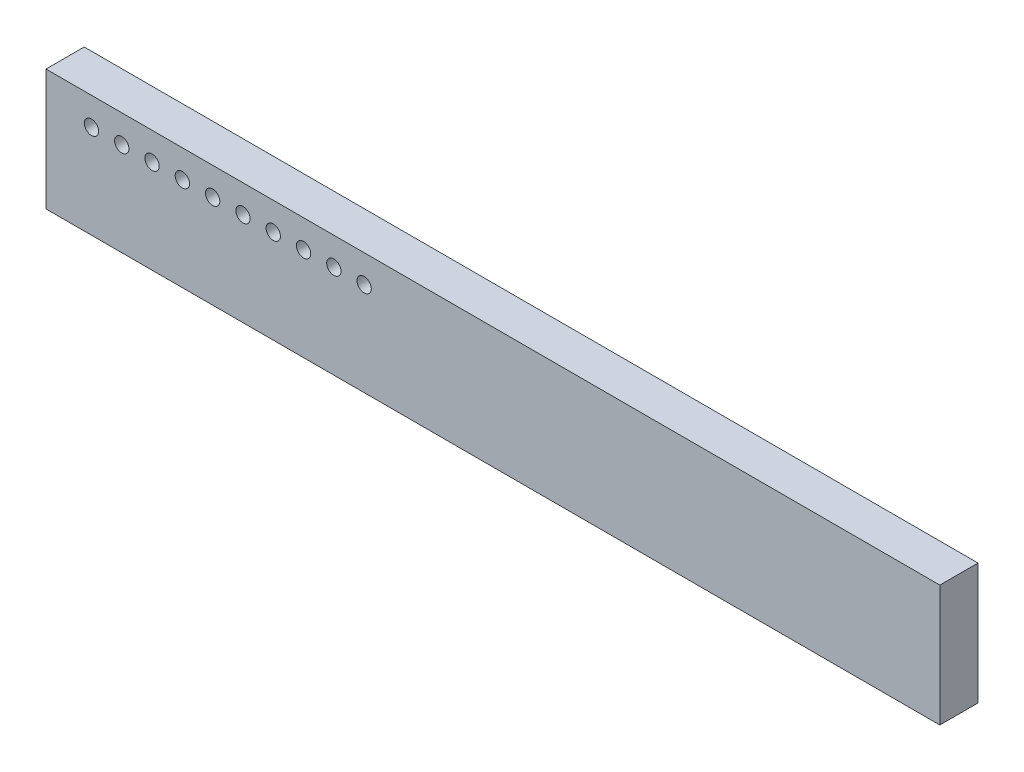
SolidWorks part; units mm, degrees
ref_plane "Front Plane" through (0, 0, 0) normal (0, 0, 1) x (1, 0, 0)
ref_plane "Top Plane" through (0, 0, 0) normal (0, 1, 0) x (1, 0, 0)
ref_plane "Right Plane" through (0, 0, 0) normal (1, 0, 0) x (0, 0, -1)
sketch "Sketch1" plane through (0, 0, 0) normal (0, 0, 1) x (1, 0, 0)
  line L1 (-18.7325, -2.54) -> (18.7325, -2.54)
  line L2 (-18.7325, -2.54) -> (-18.7325, 2.54)
  line L3 (-18.7325, 2.54) -> (18.7325, 2.54)
  line L4 (18.7325, -2.54) -> (18.7325, 2.54)
  line L5 (-18.7325, -2.54) -> (18.7325, 2.54) construction
  line L6 (-18.7325, 2.54) -> (18.7325, -2.54) construction
  point P0 (0, 0)
  dimension "D1" = 37.465
  dimension "D2" = 5.08
extrude "Boss-Extrude1" add sketch "Sketch1" along normal blind 1.6
sketch "Sketch2" plane through (0, 0, 1.6) normal (0, 0, 1) x (1, 0, 0)
  line L0 (-5.4725, 1.455) -> (-5.3225, 1.305) construction
  line L1 (-18.7325, 2.54) -> (-18.7325, -2.54) construction
  line L2 (18.7325, 2.54) -> (-18.7325, 2.54) construction
  line L4 (-5.3225, 1.455) -> (-5.4725, 1.455)
  line L5 (-5.4725, 1.455) -> (-5.4725, 1.305)
  line L6 (-5.4725, 1.305) -> (-5.3225, 1.305)
  line L7 (-5.3225, 1.305) -> (-5.3225, 1.455)
  line L8 (-5.3225, 1.455) -> (-5.4725, 1.455)
  line L9 (-5.4725, 1.455) -> (-5.4725, 1.305)
  line L10 (-5.4725, 1.305) -> (-5.3225, 1.305)
  line L11 (-5.3225, 1.305) -> (-5.3225, 1.455)
  circle A0 centre (-5.3975, 1.38) radius 0.3
  circle A1 centre (-6.6675, 1.38) radius 0.3
  circle A2 centre (-7.9375, 1.38) radius 0.3
  circle A3 centre (-9.2075, 1.38) radius 0.3
  circle A4 centre (-10.4775, 1.38) radius 0.3
  circle A5 centre (-11.7475, 1.38) radius 0.3
  circle A6 centre (-13.0175, 1.38) radius 0.3
  circle A7 centre (-14.2875, 1.38) radius 0.3
  circle A8 centre (-15.5575, 1.38) radius 0.3
  circle A9 centre (-16.8275, 1.38) radius 0.3
  dimension "D2" = 10
  dimension "D5" = 0.6
  dimension "D3" = 1.905
  dimension "D4" = 1.16
  dimension "D1" = 0
extrude "Cut-Extrude1" cut sketch "Sketch2" against normal blind 2.54
sketch "Sketch3" plane through (0, 0, 1.6) normal (0, 0, 1) x (1, 0, 0)
  line L0 (-18.7325, 2.54) -> (-16.1925, 0) construction
  line L1 (-16.1925, 0) -> (-18.7325, -2.54) construction
  line L2 (0, 2.54) -> (0, -2.54) construction
  line L3 (18.7325, 2.54) -> (-18.7325, 2.54) construction
  line L4 (-18.7325, -2.54) -> (18.7325, -2.54) construction
  line L5 (-18.7325, 2.54) -> (-18.7325, -2.54) construction
  line L6 (-18.7325, 0) -> (18.7325, 0) construction
  line L7 (18.7325, -2.54) -> (18.7325, 2.54) construction
  line L8 (18.7325, 2.54) -> (16.1925, 0) construction
  line L9 (16.1925, 0) -> (18.7325, -2.54) construction
  point P17 (15.1689, 0)
  point P21 (-15.3925, 0)
  point P24 (-9.2355, 0)
  point P25 (-3.0785, 0)
  point P26 (3.0785, 0)
  point P27 (9.2355, 0)
  point P28 (15.3925, 0)
  dimension "D1" = 32.385
  dimension "D2" = 0.8
  dimension "D4" = 0.8
  dimension "D5" = 6.157
  dimension "D6" = 3.34
  dimension "D7" = 9.497
  dimension "D8" = 15.654
  dimension "D9" = 21.811
  dimension "D10" = 27.968
  dimension "D11" = 34.125
  dimension "D3" = 6
